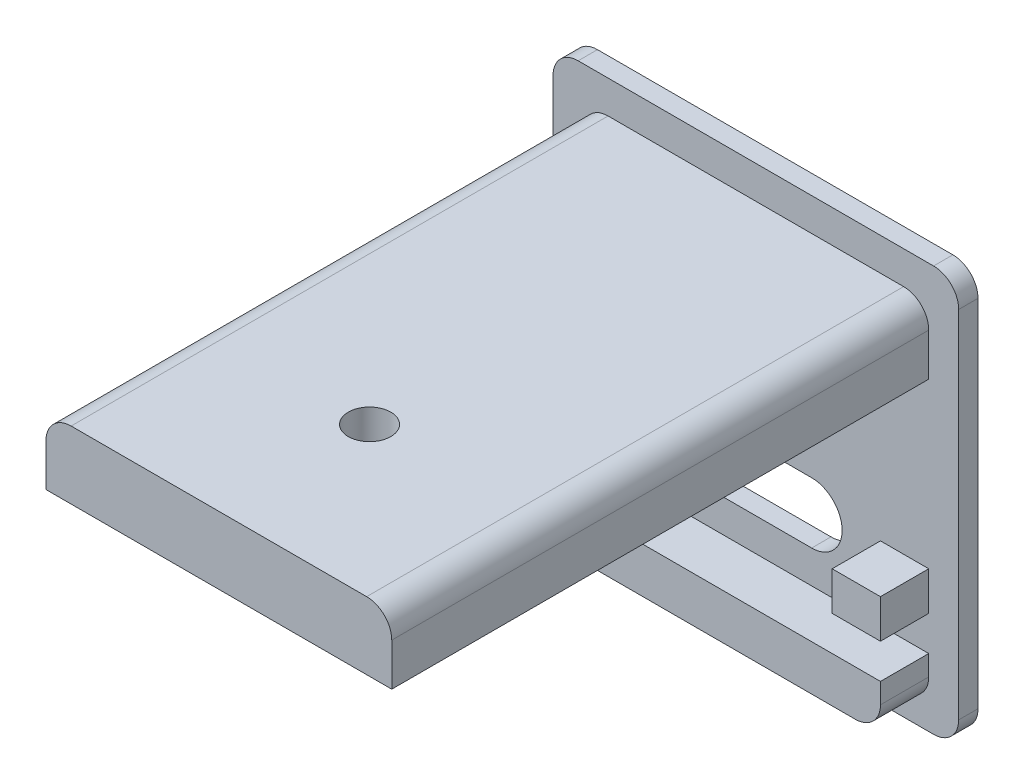
SolidWorks part; units mm, degrees
ref_plane "前视基准面" through (0, 0, 0) normal (0, 0, 1) x (1, 0, 0)
ref_plane "上视基准面" through (0, 0, 0) normal (0, 1, 0) x (1, 0, 0)
ref_plane "右视基准面" through (0, 0, 0) normal (1, 0, 0) x (0, 0, -1)
sketch "草图1" plane through (0, 0, 0) normal (0, 0, 1) x (1, 0, 0)
  line L0 (-9.2, -10.5) -> (9.2, -10.5)
  line L1 (-10.5, -9.2) -> (-10.5, 9.2)
  line L2 (-9.2, 10.5) -> (9.2, 10.5)
  line L3 (10.5, -9.2) -> (10.5, 9.2)
  line L4 (-10.5, -10.5) -> (10.5, 10.5) construction
  line L5 (-10.5, 10.5) -> (10.5, -10.5) construction
  arc A0 (-9.2, -10.5) -> (-10.5, -9.2) centre (-9.2, -9.2) cw
  arc A1 (9.2, -10.5) -> (10.5, -9.2) centre (9.2, -9.2) ccw
  arc A2 (9.2, 10.5) -> (10.5, 9.2) centre (9.2, 9.2) cw
  arc A3 (-10.5, 9.2) -> (-9.2, 10.5) centre (-9.2, 9.2) cw
  point P0 (0, 0)
  point P17 (0, 0)
  dimension "D3" = 1.3
  dimension "D1" = 21
  dimension "D2" = 21
extrude "凸台-拉伸1" add sketch "草图1" along normal blind 1
sketch "草图3" plane through (0, 0, 1) normal (0, 0, 1) x (1, 0, 0)
  line L5 (0, 0) -> (0, 4.8897) construction
  line L6 (8.95, -5.2) -> (6.45, -5.2)
  line L9 (-8.95, -3.2) -> (-6.45, -3.2)
  line L10 (-8.95, -3.2) -> (-8.95, -5.2)
  line L11 (-8.95, -5.2) -> (-6.45, -5.2)
  line L12 (-6.45, -3.2) -> (-6.45, -5.2)
  line L17 (6.45, -3.2) -> (6.45, -5.2)
  line L18 (8.95, -3.2) -> (6.45, -3.2)
  line L19 (8.95, -3.2) -> (8.95, -5.2)
  line L20 (-8.95, -7) -> (8.95, -7)
  line L21 (-10.5, 9.2) -> (-10.5, -9.2) construction
  line L22 (-9.2, -10.5) -> (9.2, -10.5) construction
  line L23 (-8.95, -7) -> (-8.95, -8.05)
  line L24 (-7.65, -9.35) -> (7.65, -9.35)
  line L25 (8.95, -7) -> (8.95, -8.05)
  arc A4 (-8.95, -8.05) -> (-7.65, -9.35) centre (-7.65, -8.05) ccw
  arc A5 (7.65, -9.35) -> (8.95, -8.05) centre (7.65, -8.05) ccw
  arc A6 (-10.5, -9.2) -> (-9.2, -10.5) centre (-9.2, -9.2) ccw construction
  point P13 (0, -7)
  dimension "D6" = 1.15
  dimension "D1" = 1.55
  dimension "D2" = 3.5
  dimension "D3" = 2
  dimension "D4" = 2.5
  dimension "D5" = 1.8
extrude "凸台-拉伸2" add sketch "草图3" along normal blind 2.5
sketch "草图2" plane through (0, 0, 1) normal (0, 0, 1) x (1, 0, 0)
  line L0 (-2.89, -3.725) -> (2.89, -3.725) construction
  line L1 (-2.89, -2.15) -> (2.89, -2.15)
  line L2 (-2.89, -5.3) -> (2.89, -5.3)
  line L4 (8.95, -7) -> (-8.95, -7) construction
  arc A0 (-2.89, -2.15) -> (-2.89, -5.3) centre (-2.89, -3.725) ccw
  arc A1 (2.89, -5.3) -> (2.89, -2.15) centre (2.89, -3.725) ccw
  point P2 (0, -3.725)
  point P7 (0, 0)
  dimension "D2" = 8.93
  dimension "D1" = 3.15
  dimension "D3" = 1.7
extrude "切除-拉伸1" cut sketch "草图2" against normal through all
sketch "草图4" plane through (0, 0, 1) normal (0, 0, 1) x (1, 0, 0)
  line L0 (-7.65, 8.8) -> (7.65, 8.8)
  line L1 (-8.95, 7.5) -> (-8.95, 5.3)
  line L2 (8.95, 7.5) -> (8.95, 5.3)
  line L3 (-8.95, 5.3) -> (8.95, 5.3)
  line L4 (9.2, 10.5) -> (-9.2, 10.5) construction
  line L5 (-8.95, -3.2) -> (-8.95, -5.2) construction
  arc A0 (7.65, 8.8) -> (8.95, 7.5) centre (7.65, 7.5) cw
  arc A1 (-7.65, 8.8) -> (-8.95, 7.5) centre (-7.65, 7.5) ccw
  arc A2 (-9.2, 10.5) -> (-10.5, 9.2) centre (-9.2, 9.2) ccw construction
  point P10 (0, 5.3)
  dimension "D1" = 1.7
  dimension "D2" = 3.5
extrude "凸台-拉伸3" add sketch "草图4" along normal blind 27.8
sketch "草图5" plane through (0, 8.8, 0) normal (0, 1, 0) x (1, 0, 0)
  line L0 (7.65, -1) -> (-7.65, -1) construction
  circle A0 centre (0, -21) radius 1.1
  point P4 (0, 0)
  dimension "D2" = 2.2
  dimension "D1" = 20
extrude "切除-拉伸2" cut sketch "草图5" against normal through all
sketch "草图6" plane through (0, 5.3, 0) normal (0, -1, 0) x (1, 0, 0)
  line L1 (1.1258, 22.95) -> (-1.1258, 22.95)
  line L2 (-1.1258, 22.95) -> (-2.2517, 21)
  line L3 (-2.2517, 21) -> (-1.1258, 19.05)
  line L4 (-1.1258, 19.05) -> (1.1258, 19.05)
  line L5 (1.1258, 19.05) -> (2.2517, 21)
  line L6 (2.2517, 21) -> (1.1258, 22.95)
  circle A0 centre (0, 21) radius 1.95 construction
  dimension "D1" = 3.9
extrude "切除-拉伸3" cut sketch "草图6" against normal blind 1.6
